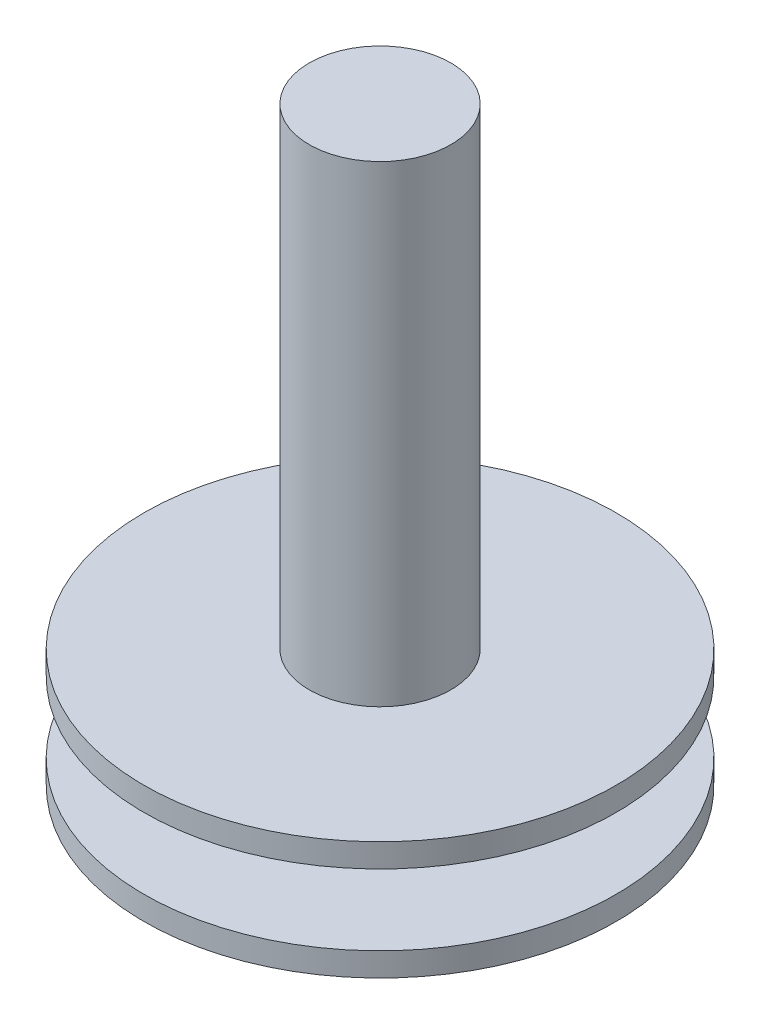
SolidWorks part; units mm, degrees
ref_plane "Front Plane" through (0, 0, 0) normal (0, 0, 1) x (1, 0, 0)
ref_plane "Top Plane" through (0, 0, 0) normal (0, 1, 0) x (1, 0, 0)
ref_plane "Right Plane" through (0, 0, 0) normal (1, 0, 0) x (0, 0, -1)
sketch "Sketch1" plane through (0, 0, 0) normal (0, 0, 1) x (1, 0, 0)
  line L0 (0, 0) -> (10, 0)
  line L1 (10, 0) -> (10, 1)
  line L2 (10, 1) -> (5, 1)
  line L3 (5, 1) -> (5, 4)
  line L4 (5, 4) -> (10, 4)
  line L5 (10, 4) -> (10, 5)
  line L6 (10, 5) -> (0, 5)
  line L7 (0, 5) -> (0, 0)
  dimension "D1" = 10
  dimension "D2" = 5
  dimension "D3" = 1
  dimension "D4" = 1
  dimension "D5" = 5
revolve "Revolve1" add sketch "Sketch1" angle 360 about L7
sketch "Sketch2" plane through (0, 5, 0) normal (0, 1, 0) x (1, 0, 0)
  circle A0 centre (0, 0) radius 3
  dimension "D1" = 6
extrude "Boss-Extrude1" add sketch "Sketch2" along normal blind 20
